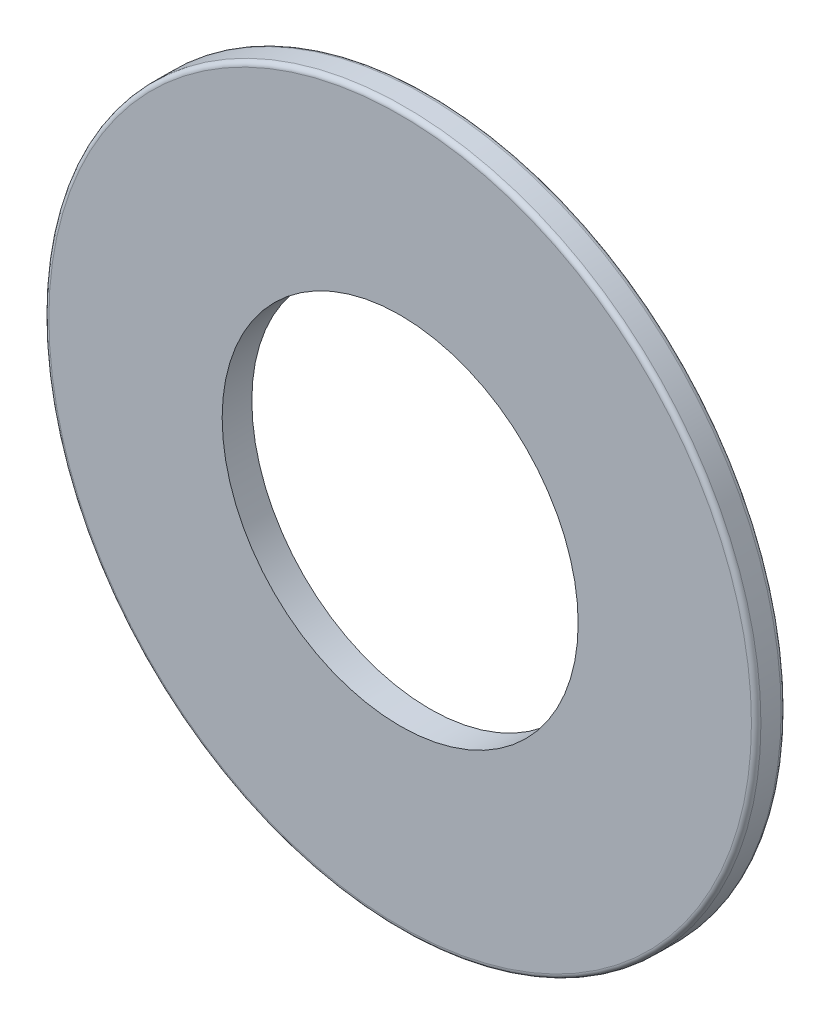
SolidWorks part; units mm, degrees
material "Tin Bearing Bronze"
ref_plane "Front Plane" through (0, 0, 0) normal (0, 0, 1) x (1, 0, 0)
ref_plane "Top Plane" through (0, 0, 0) normal (0, 1, 0) x (1, 0, 0)
ref_plane "Right Plane" through (0, 0, 0) normal (1, 0, 0) x (0, 0, -1)
sketch "Sketch1" plane through (0, 0, 0) normal (0, 0, 1) x (1, 0, 0)
  circle A0 centre (0, 0) radius 4.7625
  circle A1 centre (0, 0) radius 9.525
  dimension "D1" = 19.05
  dimension "D2" = 9.525
extrude "Boss-Extrude1" add sketch "Sketch1" along normal blind 0.7937
fillet "Fillet1" radius 0.127 2 edges at (9.525, 0, 0) (9.525, 0, 0.7937)
